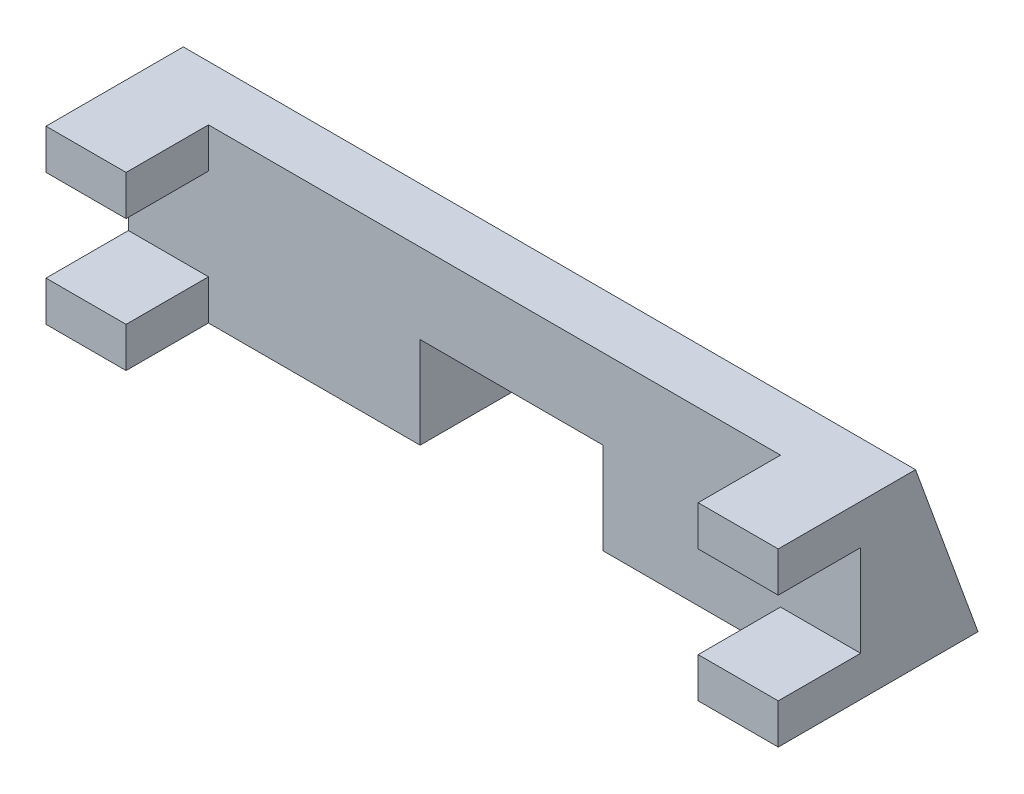
SolidWorks part; units mm, degrees
ref_plane "Front Plane" through (0, 0, 0) normal (0, 0, 1) x (1, 0, 0)
ref_plane "Top Plane" through (0, 0, 0) normal (0, 1, 0) x (1, 0, 0)
ref_plane "Right Plane" through (0, 0, 0) normal (1, 0, 0) x (0, 0, -1)
sketch "Sketch1" plane through (0, 0, 0) normal (1, 0, 0) x (0, 0, -1)
  line L0 (0.3592, -3.3171) -> (0.3592, 0.1829)
  line L1 (12.3592, -14.8171) -> (0.3592, -14.8171)
  line L3 (12.3592, 0.1829) -> (0.3592, 0.1829)
  line L4 (0.3592, -14.8171) -> (0.3592, -11.3171)
  line L5 (0.3592, -11.3171) -> (7.5592, -11.3171)
  line L6 (12.3592, 0.1829) -> (17113.3663, -46984.4482) construction
  line L7 (0.3592, -3.3171) -> (7.5592, -3.3171)
  line L8 (7.5592, -11.3171) -> (7.5592, -3.3171)
  line L9 (12.3592, 0.1829) -> (17.8187, -14.8171)
  line L10 (12.3592, 0.1829) -> (12.484, 0.1829) construction
  line L11 (17.8187, -14.8171) -> (12.3592, -14.8171)
  dimension "D1" = 15
  dimension "D2" = 8
  dimension "D3" = 3.5
  dimension "D4" = 7.2
  dimension "D5" = 12
extrude "Boss-Extrude1" add sketch "Sketch1" along normal blind 64
sketch "Sketch2" plane through (0, -11.3171, 0) normal (0, 1, 0) x (1, 0, 0)
  line L0 (64, 7.5592) -> (0, 7.5592) construction
  line L1 (7, 7.5592) -> (57, 7.5592)
  line L2 (7, 7.5592) -> (7, 0.3592)
  line L3 (7, 0.3592) -> (57, 0.3592)
  line L4 (57, 7.5592) -> (57, 0.3592)
  line L5 (64, 0.3592) -> (0, 0.3592) construction
  line L7 (0, 7.5592) -> (0, 0.3592) construction
  dimension "D1" = 50
  dimension "D2" = 7
extrude "Cut-Extrude1" cut sketch "Sketch2" against normal through all and the other way through all
sketch "Sketch3" plane through (0, 0, -7.5592) normal (0, 0, 1) x (1, 0, 0)
  line L0 (57, -14.8171) -> (7, -14.8171) construction
  line L1 (25.5, -6.8171) -> (41.5, -6.8171)
  line L2 (25.5, -6.8171) -> (25.5, -14.8171)
  line L3 (25.5, -14.8171) -> (41.5, -14.8171)
  line L4 (41.5, -6.8171) -> (41.5, -14.8171)
  line L5 (57, -14.8171) -> (57, -11.3171) construction
  dimension "D1" = 16
  dimension "D2" = 15.5
  dimension "D3" = 8
extrude "Cut-Extrude2" cut sketch "Sketch3" against normal blind 64
